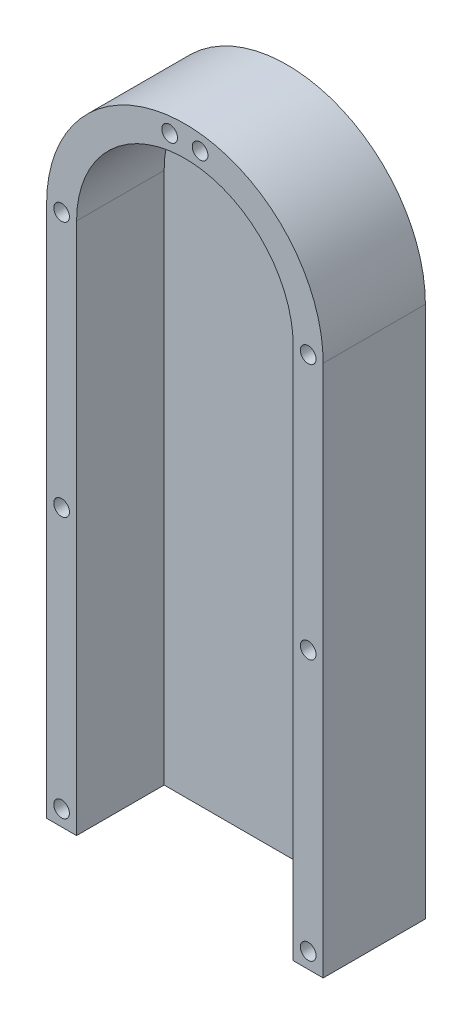
SolidWorks part; units mm, degrees
ref_plane "Front Plane" through (0, 0, 0) normal (0, 0, 1) x (1, 0, 0)
ref_plane "Top Plane" through (0, 0, 0) normal (0, 1, 0) x (1, 0, 0)
ref_plane "Right Plane" through (0, 0, 0) normal (1, 0, 0) x (0, 0, -1)
sketch "Sketch2" plane through (0, 0, 0) normal (0, 0, 1) x (1, 0, 0)
  line L0 (54.5827, -59.5829) -> (54.5827, 171.3946)
  line L1 (-5.4173, 171.3946) -> (-5.4173, -59.5829)
  arc A0 (-5.4173, -59.5829) -> (54.5827, -59.5829) centre (24.5827, -59.5829) ccw
  arc A1 (54.5827, 171.3946) -> (-5.4173, 171.3946) centre (24.5827, 171.3946) ccw
  circle A2 centre (27.8827, 197.9403) radius 1.7
  circle A3 centre (-2.1673, -59.5829) radius 1.7
  circle A4 centre (5.6676, -78.498) radius 1.7
  circle A5 centre (21.1827, -86.116) radius 1.7
  circle A6 centre (51.3327, 171.3946) radius 1.7
  circle A9 centre (-2.1673, 59.3059) radius 1.7
  circle A10 centre (27.9827, -86.116) radius 1.7
  circle A12 centre (-2.1673, 171.3946) radius 1.7
  circle A13 centre (51.3327, 115.9059) radius 1.7
  circle A14 centre (-2.1673, 115.9059) radius 1.7
  circle A16 centre (43.4978, -78.498) radius 1.7
  circle A17 centre (51.3327, -59.5829) radius 1.7
  circle A18 centre (51.3327, -34.0941) radius 1.7
  circle A19 centre (-2.1673, -34.0941) radius 1.7
  circle A20 centre (51.3327, -4.0941) radius 1.7
  circle A21 centre (-2.1673, -4.0941) radius 1.7
  circle A22 centre (51.3327, 25.9059) radius 1.7
  circle A23 centre (-2.1673, 25.9059) radius 1.7
  circle A26 centre (21.2827, 197.9403) radius 1.7
  circle A27 centre (51.3327, 52.5059) radius 1.7
  circle A28 centre (51.3327, 59.3059) radius 1.7
  circle A29 centre (-2.1673, 52.5059) radius 1.7
extrude "Boss-Extrude1" add sketch "Sketch2" along normal blind 3.175
sketch "Sketch3" plane through (0, 0, 3.175) normal (0, 0, 1) x (1, 0, 0)
  line L0 (-5.4173, 55.9059) -> (54.5827, 55.9059)
  line L1 (-5.4173, 171.3946) -> (-5.4173, -59.5829) construction
  line L2 (54.5827, -59.5829) -> (54.5827, 171.3946) construction
  line L3 (54.5827, 55.9059) -> (54.5827, -104.6501)
  line L4 (54.5827, -104.6501) -> (-5.4173, -104.6501)
  line L5 (-5.4173, -104.6501) -> (-5.4173, 55.9059)
extrude "Cut-Extrude1" cut sketch "Sketch3" against normal through all
sketch "Sketch4" plane through (0, 0, 3.175) normal (0, 0, 1) x (1, 0, 0)
  line L0 (48.0827, 171.3946) -> (48.0827, 55.9059)
  line L1 (1.0827, 171.3946) -> (1.0827, 55.9059)
  line L2 (48.0827, 55.9059) -> (54.5827, 55.9059)
  line L3 (-5.4173, 55.9059) -> (54.5827, 55.9059)
  line L4 (54.5827, 55.9059) -> (54.5827, 171.3946)
  line L5 (-5.4173, 171.3946) -> (-5.4173, 55.9059)
  line L6 (-5.4173, 55.9059) -> (1.0827, 55.9059)
  line L7 (54.5827, 55.9059) -> (54.5827, 171.3946)
  line L8 (-5.4173, 171.3946) -> (-5.4173, 55.9059)
  circle A0 centre (-2.1673, 115.9059) radius 1.7 construction
  arc A1 (54.5827, 171.3946) -> (-5.4173, 171.3946) centre (24.5827, 171.3946) ccw
  arc A2 (54.5827, 171.3946) -> (-5.4173, 171.3946) centre (24.5827, 171.3946) ccw
  circle A3 centre (-2.1673, 59.3059) radius 1.7 construction
  circle A4 centre (51.3327, 59.3059) radius 1.7 construction
  circle A5 centre (51.3327, 115.9059) radius 1.7 construction
  circle A6 centre (51.3327, 171.3946) radius 1.7 construction
  circle A7 centre (27.8827, 197.9403) radius 1.7 construction
  circle A8 centre (21.2827, 197.9403) radius 1.7 construction
  circle A9 centre (-2.1673, 171.3946) radius 1.7 construction
  circle A10 centre (-2.1673, 115.9059) radius 1.7
  circle A11 centre (-2.1673, 59.3059) radius 1.7
  circle A12 centre (51.3327, 59.3059) radius 1.7
  circle A13 centre (51.3327, 115.9059) radius 1.7
  circle A14 centre (51.3327, 171.3946) radius 1.7
  circle A15 centre (27.8827, 197.9403) radius 1.7
  circle A16 centre (21.2827, 197.9403) radius 1.7
  circle A17 centre (-2.1673, 171.3946) radius 1.7
  arc A18 (48.0827, 171.3946) -> (1.0827, 171.3946) centre (24.5827, 171.3946) ccw
  dimension "D2" = 47
  dimension "D1" = 0
extrude "Boss-Extrude2" add sketch "Sketch4" along normal blind 19
